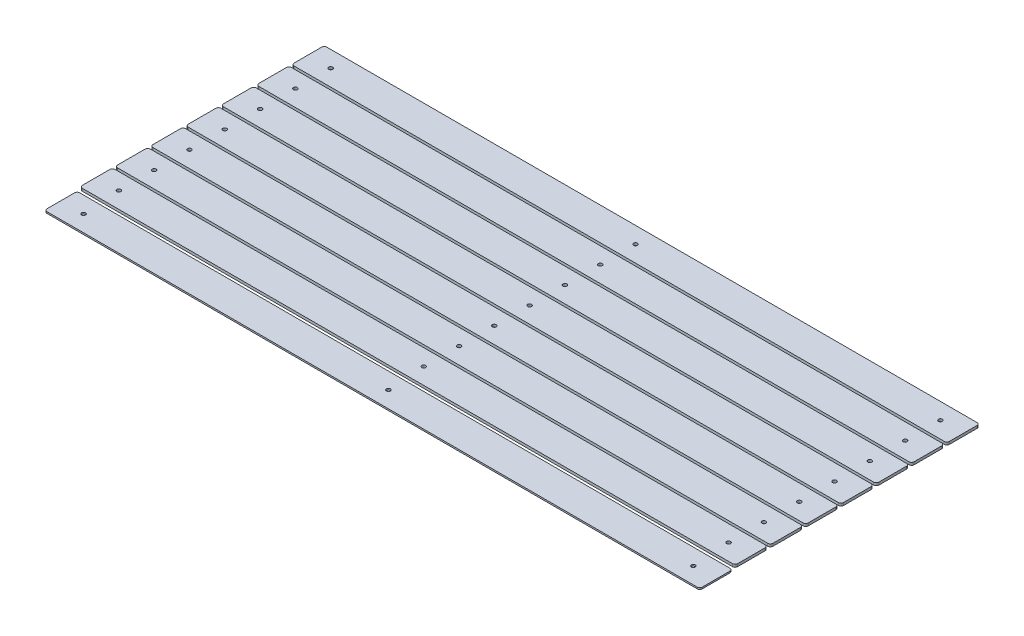
SolidWorks part; units mm, degrees
ref_plane "Front Plane" through (0, 0, 0) normal (0, 0, 1) x (1, 0, 0)
ref_plane "Top Plane" through (0, 0, 0) normal (0, 1, 0) x (1, 0, 0)
ref_plane "Right Plane" through (0, 0, 0) normal (1, 0, 0) x (0, 0, -1)
sketch "Sketch1" plane through (0, 0, 0) normal (0, 1, 0) x (1, 0, 0)
  line L1 (-318.2832, -15.875) -> (318.2832, -15.875)
  line L2 (-318.2832, -15.875) -> (-318.2832, 15.875)
  line L3 (-318.2832, 15.875) -> (318.2832, 15.875)
  line L4 (318.2832, -15.875) -> (318.2832, 15.875)
  line L5 (-318.2832, -15.875) -> (318.2832, 15.875) construction
  line L6 (-318.2832, 15.875) -> (318.2832, -15.875) construction
  point P0 (0, 0)
  dimension "D1" = 31.75
  dimension "D2" = 636.5663
extrude "Boss-Extrude1" add sketch "Sketch1" along normal blind 1.524
sketch "Sketch2" plane through (0, 1.524, 0) normal (0, 1, 0) x (1, 0, 0)
  line L0 (-318.2832, 15.875) -> (318.2832, -15.875) construction
  line L1 (-296.164, 0) -> (296.164, 0) construction
  circle A0 centre (-296.164, 0) radius 1.905
  circle A1 centre (296.164, 0) radius 1.905
  circle A2 centre (0, 0) radius 1.905
  point P8 (0, 0)
  dimension "D2" = 3.81
  dimension "D1" = 592.328
extrude "Cut-Extrude1" cut sketch "Sketch2" against normal through all
fillet "Fillet1" radius 2.54 4 edges at (318.2832, 0.762, 15.875) (318.2832, 0.762, -15.875) (-318.2832, 0.762, 15.875) (-318.2832, 0.762, -15.875)
sketch "Sketch3" plane through (0, 1.524, 0) normal (0, 1, 0) x (1, 0, 0)
  line L0 (-315.7432, 18.415) -> (315.7432, 18.415)
  line L1 (318.2832, 20.955) -> (318.2832, 47.625)
  line L2 (315.7432, 50.165) -> (-315.7432, 50.165)
  line L3 (-318.2832, 47.625) -> (-318.2832, 20.955)
  line L12 (-315.7432, 52.705) -> (315.7432, 52.705)
  line L13 (318.2832, 55.245) -> (318.2832, 81.915)
  line L14 (315.7432, 84.455) -> (-315.7432, 84.455)
  line L15 (-318.2832, 81.915) -> (-318.2832, 55.245)
  line L16 (-315.7432, 86.995) -> (315.7432, 86.995)
  line L17 (318.2832, 89.535) -> (318.2832, 116.205)
  line L18 (315.7432, 118.745) -> (-315.7432, 118.745)
  line L19 (-318.2832, 116.205) -> (-318.2832, 89.535)
  line L20 (-315.7432, 121.285) -> (315.7432, 121.285)
  line L21 (318.2832, 123.825) -> (318.2832, 150.495)
  line L22 (315.7432, 153.035) -> (-315.7432, 153.035)
  line L23 (-318.2832, 150.495) -> (-318.2832, 123.825)
  line L24 (-315.7432, 155.575) -> (315.7432, 155.575)
  line L25 (318.2832, 158.115) -> (318.2832, 184.785)
  line L26 (315.7432, 187.325) -> (-315.7432, 187.325)
  line L27 (-318.2832, 184.785) -> (-318.2832, 158.115)
  line L28 (-315.7432, 189.865) -> (315.7432, 189.865)
  line L29 (318.2832, 192.405) -> (318.2832, 219.075)
  line L30 (315.7432, 221.615) -> (-315.7432, 221.615)
  line L31 (-318.2832, 219.075) -> (-318.2832, 192.405)
  line L32 (-315.7432, 224.155) -> (315.7432, 224.155)
  line L33 (318.2832, 226.695) -> (318.2832, 253.365)
  line L34 (315.7432, 255.905) -> (-315.7432, 255.905)
  line L35 (-318.2832, 253.365) -> (-318.2832, 226.695)
  circle A14 centre (296.164, 34.29) radius 1.905
  arc A15 (315.7432, 18.415) -> (318.2832, 20.955) centre (315.7432, 20.955) ccw
  arc A16 (318.2832, 47.625) -> (315.7432, 50.165) centre (315.7432, 47.625) ccw
  arc A17 (-315.7432, 50.165) -> (-318.2832, 47.625) centre (-315.7432, 47.625) ccw
  arc A18 (-318.2832, 20.955) -> (-315.7432, 18.415) centre (-315.7432, 20.955) ccw
  circle A19 centre (0, 34.29) radius 1.905
  circle A20 centre (-296.164, 34.29) radius 1.905
  circle A21 centre (296.164, 68.58) radius 1.905
  arc A22 (315.7432, 52.705) -> (318.2832, 55.245) centre (315.7432, 55.245) ccw
  arc A23 (318.2832, 81.915) -> (315.7432, 84.455) centre (315.7432, 81.915) ccw
  arc A24 (-315.7432, 84.455) -> (-318.2832, 81.915) centre (-315.7432, 81.915) ccw
  arc A25 (-318.2832, 55.245) -> (-315.7432, 52.705) centre (-315.7432, 55.245) ccw
  circle A26 centre (0, 68.58) radius 1.905
  circle A27 centre (-296.164, 68.58) radius 1.905
  circle A28 centre (296.164, 102.87) radius 1.905
  arc A29 (315.7432, 86.995) -> (318.2832, 89.535) centre (315.7432, 89.535) ccw
  arc A30 (318.2832, 116.205) -> (315.7432, 118.745) centre (315.7432, 116.205) ccw
  arc A31 (-315.7432, 118.745) -> (-318.2832, 116.205) centre (-315.7432, 116.205) ccw
  arc A32 (-318.2832, 89.535) -> (-315.7432, 86.995) centre (-315.7432, 89.535) ccw
  circle A33 centre (0, 102.87) radius 1.905
  circle A34 centre (-296.164, 102.87) radius 1.905
  circle A35 centre (296.164, 137.16) radius 1.905
  arc A36 (315.7432, 121.285) -> (318.2832, 123.825) centre (315.7432, 123.825) ccw
  arc A37 (318.2832, 150.495) -> (315.7432, 153.035) centre (315.7432, 150.495) ccw
  arc A38 (-315.7432, 153.035) -> (-318.2832, 150.495) centre (-315.7432, 150.495) ccw
  arc A39 (-318.2832, 123.825) -> (-315.7432, 121.285) centre (-315.7432, 123.825) ccw
  circle A40 centre (0, 137.16) radius 1.905
  circle A41 centre (-296.164, 137.16) radius 1.905
  circle A42 centre (296.164, 171.45) radius 1.905
  arc A43 (315.7432, 155.575) -> (318.2832, 158.115) centre (315.7432, 158.115) ccw
  arc A44 (318.2832, 184.785) -> (315.7432, 187.325) centre (315.7432, 184.785) ccw
  arc A45 (-315.7432, 187.325) -> (-318.2832, 184.785) centre (-315.7432, 184.785) ccw
  arc A46 (-318.2832, 158.115) -> (-315.7432, 155.575) centre (-315.7432, 158.115) ccw
  circle A47 centre (0, 171.45) radius 1.905
  circle A48 centre (-296.164, 171.45) radius 1.905
  circle A49 centre (296.164, 205.74) radius 1.905
  arc A50 (315.7432, 189.865) -> (318.2832, 192.405) centre (315.7432, 192.405) ccw
  arc A51 (318.2832, 219.075) -> (315.7432, 221.615) centre (315.7432, 219.075) ccw
  arc A52 (-315.7432, 221.615) -> (-318.2832, 219.075) centre (-315.7432, 219.075) ccw
  arc A53 (-318.2832, 192.405) -> (-315.7432, 189.865) centre (-315.7432, 192.405) ccw
  circle A54 centre (0, 205.74) radius 1.905
  circle A55 centre (-296.164, 205.74) radius 1.905
  circle A56 centre (296.164, 240.03) radius 1.905
  arc A57 (315.7432, 224.155) -> (318.2832, 226.695) centre (315.7432, 226.695) ccw
  arc A58 (318.2832, 253.365) -> (315.7432, 255.905) centre (315.7432, 253.365) ccw
  arc A59 (-315.7432, 255.905) -> (-318.2832, 253.365) centre (-315.7432, 253.365) ccw
  arc A60 (-318.2832, 226.695) -> (-315.7432, 224.155) centre (-315.7432, 226.695) ccw
  circle A61 centre (0, 240.03) radius 1.905
  circle A62 centre (-296.164, 240.03) radius 1.905
extrude "Boss-Extrude2" add sketch "Sketch3" along normal blind 2.54 separate body
